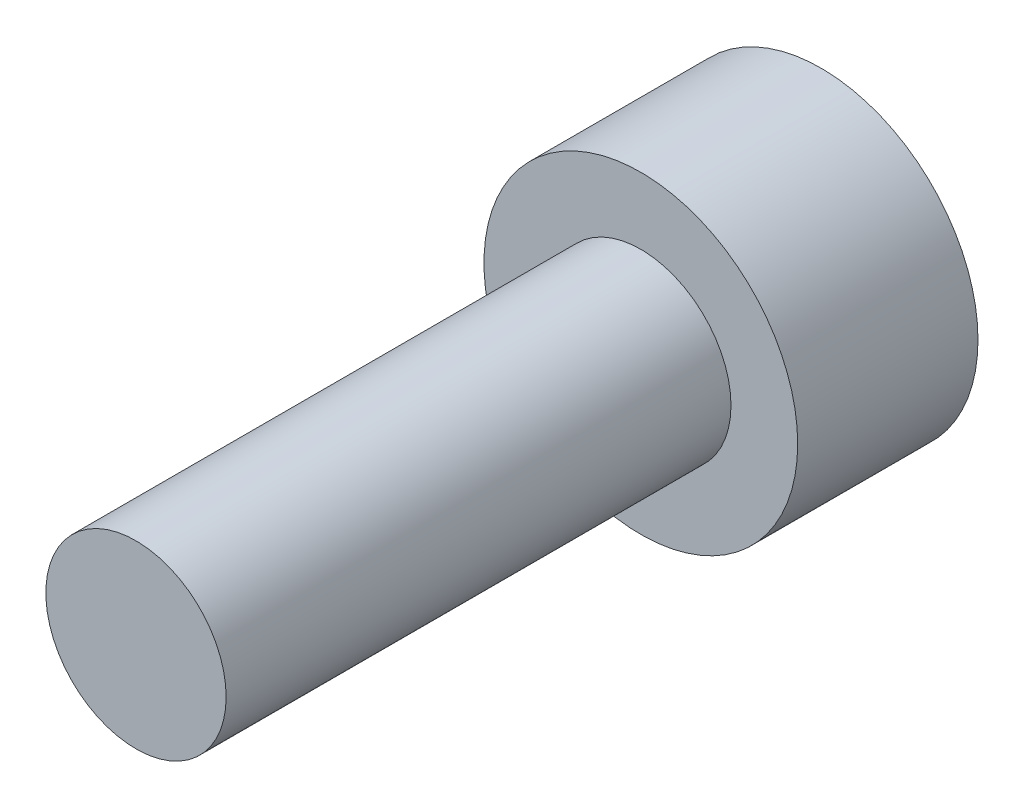
SolidWorks part; units mm, degrees
ref_plane "前视基准面" through (0, 0, 0) normal (0, 0, 1) x (1, 0, 0)
ref_plane "上视基准面" through (0, 0, 0) normal (0, 1, 0) x (1, 0, 0)
ref_plane "右视基准面" through (0, 0, 0) normal (1, 0, 0) x (0, 0, -1)
sketch "草图1" plane through (0, 0, 0) normal (0, 0, 1) x (1, 0, 0)
  circle A0 centre (0, 0) radius 4.35
  dimension "D1" = 8.7
extrude "凸台-拉伸1" add sketch "草图1" along normal blind 5
sketch "草图2" plane through (0, 0, 5) normal (0, 0, 1) x (1, 0, 0)
  circle A0 centre (0, 0) radius 2.5
  dimension "D1" = 5
extrude "凸台-拉伸2" add sketch "草图2" along normal blind 14
